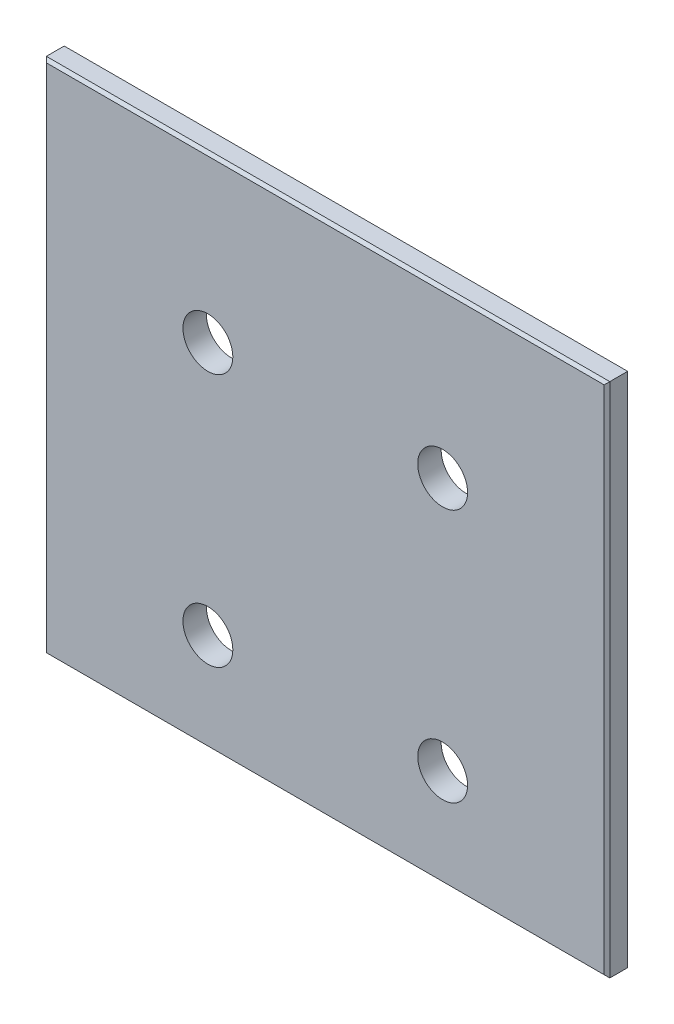
SolidWorks part; units mm, degrees
material "ASTM A36 Steel"
ref_plane "Front" through (0, 0, 0) normal (0, 0, 1) x (1, 0, 0)
ref_plane "Top" through (0, 0, 0) normal (0, 1, 0) x (1, 0, 0)
ref_plane "Right" through (0, 0, 0) normal (1, 0, 0) x (0, 0, -1)
sketch "Sketch1" plane through (0, 0, 0) normal (0, 0, 1) x (1, 0, 0)
  line L1 (-76.2, 69.85) -> (76.2, 69.85)
  line L2 (-76.2, 69.85) -> (-76.2, -69.85)
  line L3 (-76.2, -69.85) -> (76.2, -69.85)
  line L4 (76.2, 69.85) -> (76.2, -69.85)
  point P4 (-76.2, 0)
  point P5 (0, 69.85)
  dimension "D1" = 139.7
  dimension "D2" = 152.4
extrude "Extrude1" add sketch "Sketch1" along normal blind 6.35
chamfer "Chamfer1" distance 0.762 angle 45 8 edges at (0, -69.85, 0) (-76.2, 0, 0) (0, 69.85, 0) (76.2, 0, 0) (0, -69.85, 6.35) (76.2, 0, 6.35) (0, 69.85, 6.35) (-76.2, 0, 6.35)
hole_wizard "1/2 Clearance Hole1" positions "Sketch3" profile "Sketch2" hole size "1/2" standard "Ansi Inch" end condition through all
sketch "Sketch3" plane through (0, 0, 6.35) normal (0, 0, 1) x (1, 0, 0)
  line L0 (-76.2, -69.85) -> (-76.2, 69.85) construction
  line L1 (-76.2, 69.85) -> (76.2, 69.85) construction
  line L2 (-31.75, -43.18) -> (31.75, -43.18) construction
  line L3 (31.75, -43.18) -> (31.75, 25.4) construction
  line L4 (31.75, 25.4) -> (-31.75, 25.4) construction
  line L5 (-31.75, 25.4) -> (-31.75, -43.18) construction
  point P0 (-31.75, 25.4)
  point P5 (31.75, 25.4)
  point P7 (-31.75, -43.18)
  point P9 (31.75, -43.18)
  point P23 (0, 25.4)
  dimension "D1" = 44.45
  dimension "D2" = 44.45
  dimension "D3" = 113.03
sketch "Sketch2" plane through (-31.75, 25.4, 6.35) normal (1, 0, 0) x (0, -1, 0)
  line L0 (0, 0) -> (0, 6.35)
  line L1 (0, 6.35) -> (6.7462, 6.35)
  line L2 (6.7462, 6.35) -> (6.7462, 0)
  line L5 (6.7462, 0) -> (0, 0)
  line L11 (0, -6.35) -> (0, 107.95) construction
  dimension "Thru Hole Dia." = 13.4925
  dimension "Thru Hole Depth" = 6.35
